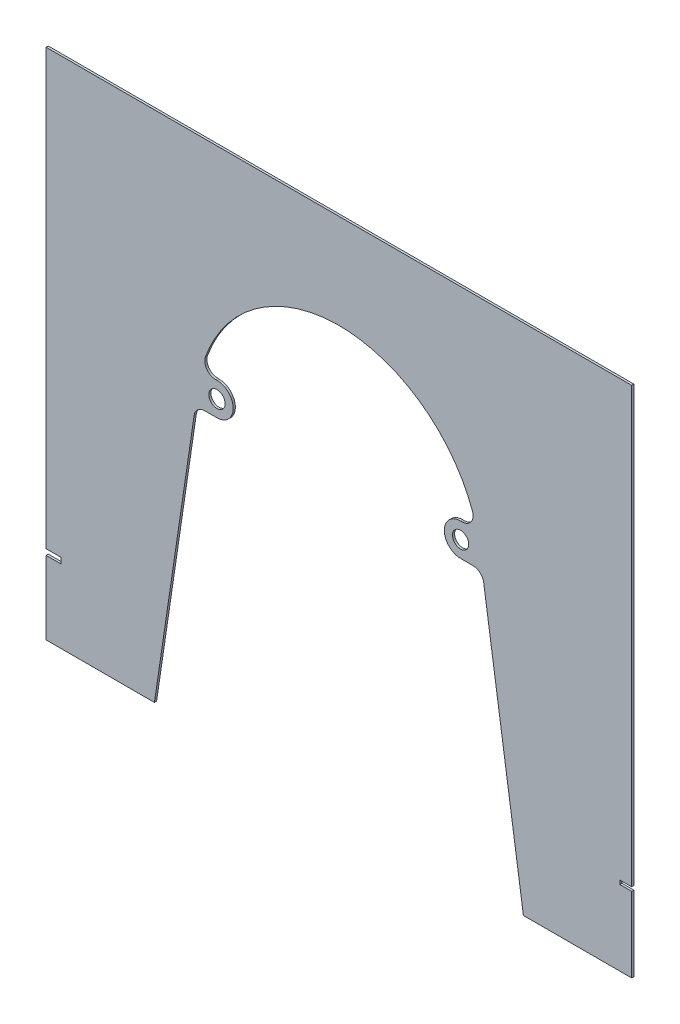
SolidWorks part; units mm, degrees
ref_plane "Front Plane" through (0, 0, 0) normal (0, 0, 1) x (1, 0, 0)
ref_plane "Top Plane" through (0, 0, 0) normal (0, 1, 0) x (1, 0, 0)
ref_plane "Right Plane" through (0, 0, 0) normal (1, 0, 0) x (0, 0, -1)
sketch "Sketch1" plane through (0, 0, 0) normal (0, 0, 1) x (1, 0, 0)
  line L0 (325.1018, -276.7456) -> (325.1018, -188.7611)
  line L1 (325.1018, 325.138) -> (-361.5506, 325.138)
  line L2 (-361.5506, 325.138) -> (-361.5506, -184.1703)
  line L3 (-361.5506, -276.7456) -> (-234.5506, -276.7456)
  line L4 (198.1018, -276.7456) -> (325.1018, -276.7456)
  line L5 (124.4188, 87.0859) -> (126.4048, 87.0859)
  line L6 (124.4188, 48.9859) -> (138.9668, 48.9859)
  line L7 (-161.2538, 87.0859) -> (-162.8538, 87.0859)
  line L8 (-161.2538, 48.9859) -> (-175.4157, 48.9859)
  line L9 (-361.5506, -184.1703) -> (-344.3677, -184.1703)
  line L10 (-344.3677, -184.1703) -> (-344.3677, -190.8357)
  line L11 (-344.3677, -190.8357) -> (-361.5506, -190.8357)
  line L12 (325.1018, -184.1703) -> (311.1474, -184.1703)
  line L13 (311.1474, -184.1703) -> (311.1474, -188.7611)
  line L14 (311.1474, -188.7611) -> (325.1018, -188.7611)
  line L15 (325.1018, -184.1703) -> (325.1018, 325.138)
  line L16 (-361.5506, -190.8357) -> (-361.5506, -276.7456)
  circle A0 centre (-161.2538, 68.0359) radius 9.5925
  circle A1 centre (124.4188, 68.0359) radius 9.525
  arc A2 (124.4188, 87.0859) -> (124.4188, 48.9859) centre (124.4188, 68.0359) ccw
  arc A3 (138.9668, 48.9859) -> (151.5316, 38.1338) centre (138.9668, 36.2859) cw
  arc A4 (126.4048, 87.0859) -> (138.34, 104.1264) centre (126.4048, 99.7859) ccw
  arc A5 (-161.2538, 48.9859) -> (-161.2538, 87.0859) centre (-161.2538, 68.0359) ccw
  arc A6 (-175.4157, 48.9859) -> (-187.9805, 38.1338) centre (-175.4157, 36.2859) ccw
  arc A7 (-162.8538, 87.0859) -> (-174.789, 104.1264) centre (-162.8538, 99.7859) cw
  spline S0 degree 3 poles (138.34, 104.1264) (138.1555, 104.6337) (137.9685, 105.1403) (136.8785, 108.0505) (135.442, 111.6348) (133.8736, 115.1853) (132.7983, 117.5447) (132.2449, 118.7222) (129.4145, 124.5671) (126.9494, 129.1017) (121.6305, 137.8979) (118.7767, 142.1594) (112.6865, 150.4133) (107.8319, 156.4021) (102.5402, 162.0835) (99.8196, 164.8717) (98.9003, 165.7922) (97.0462, 167.6061) (96.1103, 168.5006) (91.3866, 172.9114) (87.4665, 176.2426) (79.3519, 182.5216) (75.1575, 185.4695) (66.4957, 190.9836) (62.0283, 193.5498) (55.1152, 197.1028) (52.7709, 198.2394) (48.0579, 200.3902) (45.6844, 201.407) (38.5136, 204.2848) (33.6663, 205.9736) (23.84, 208.8991) (18.861, 210.1354) (11.293, 211.6478) (8.7537, 212.0949) (4.9196, 212.6788) (3.6374, 212.859) (1.0644, 213.1901) (-0.2274, 213.3411) (-4.1047, 213.7488) (-6.6939, 213.9603) (-10.5844, 214.1882) (-11.8823, 214.2492) (-14.4802, 214.3423) (-15.78, 214.3757) (-18.3798, 214.4057) (-19.6799, 214.392) (-22.279, 214.3333) (-23.5784, 214.2892) (-27.473, 214.1134) (-30.0649, 213.9372) (-35.2395, 213.4643) (-37.826, 213.1671) (-42.9603, 212.4563) (-45.5103, 212.0428) (-53.1099, 210.6304) (-58.1091, 209.4601) (-67.9746, 206.6672) (-72.8409, 205.0447) (-80.0396, 202.2683) (-83.6138, 200.7942) (-87.1495, 199.1894) (-89.498, 198.0902) (-90.6694, 197.5252) (-96.4848, 194.6361) (-100.9942, 192.1257) (-109.7381, 186.7226) (-113.9727, 183.8299) (-122.1678, 177.6629) (-126.1281, 174.3883) (-131.8575, 169.1828) (-133.732, 167.3985) (-136.4902, 164.6475) (-137.4006, 163.7181) (-139.1941, 161.8444) (-140.0785, 160.8988) (-144.4391, 156.1282) (-147.732, 152.1746) (-153.9349, 143.9988) (-156.8447, 139.7766) (-162.2769, 131.0606) (-164.7993, 126.5667) (-168.2831, 119.6158) (-169.396, 117.2597) (-171.4992, 112.5242) (-172.4922, 110.1398) (-173.8959, 106.539) (-174.3496, 105.3347) (-174.789, 104.1264) knots 0.295231 0.295231 0.295231 0.295231 0.296875 0.296875 0.304687 0.308594 0.308594 0.3125 0.3125 0.328125 0.328125 0.34375 0.34375 0.359375 0.367187 0.367187 0.371094 0.371094 0.375 0.375 0.390625 0.390625 0.40625 0.40625 0.421875 0.421875 0.429687 0.429687 0.4375 0.4375 0.453125 0.453125 0.46875 0.46875 0.476562 0.476562 0.480469 0.480469 0.484375 0.484375 0.492187 0.492187 0.496094 0.496094 0.5 0.5 0.503906 0.503906 0.507812 0.507812 0.515625 0.515625 0.523437 0.523437 0.53125 0.53125 0.546875 0.546875 0.5625 0.5625 0.570312 0.574219 0.574219 0.578125 0.578125 0.59375 0.59375 0.609375 0.609375 0.625 0.625 0.632812 0.632812 0.636719 0.636719 0.640625 0.640625 0.65625 0.65625 0.671875 0.671875 0.6875 0.6875 0.695312 0.695312 0.703125 0.703125 0.707031 0.707031 0.707031 0.707031
  spline S1 degree 3 poles (-187.9805, 38.1338) (-188.2749, 36.1321) (-188.5693, 34.1304) (-190.3694, 21.89) (-191.8763, 11.6514) (-196.4044, -19.0634) (-199.4282, -39.5391) (-205.4834, -80.4895) (-208.5158, -100.964) (-219.215, -173.2076) (-226.8819, -224.9767) (-234.5506, -276.7456) knots 0.775141 0.775141 0.775141 0.775141 0.78125 0.78125 0.8125 0.8125 0.875 0.875 0.9375 0.9375 1.095529 1.095529 1.095529 1.095529
  spline S2 degree 3 poles (198.1018, -276.7456) (190.4572, -225.1402) (182.8146, -173.5345) (172.1638, -101.6178) (169.1556, -81.3068) (163.1484, -40.6834) (160.1487, -20.3711) (155.6562, 10.0984) (154.161, 20.2552) (152.2887, 32.9861) (151.9102, 35.5599) (151.5316, 38.1338) knots -0.096298 -0.096298 -0.096298 -0.096298 0.0625 0.0625 0.125 0.125 0.1875 0.1875 0.21875 0.21875 0.226669 0.226669 0.226669 0.226669
  dimension "D3" = 12.7
  dimension "D4" = 12.7
  dimension "D1" = 127
  dimension "D2" = 127
extrude "Boss-Extrude1" add sketch "Sketch1" along normal blind 2.54
